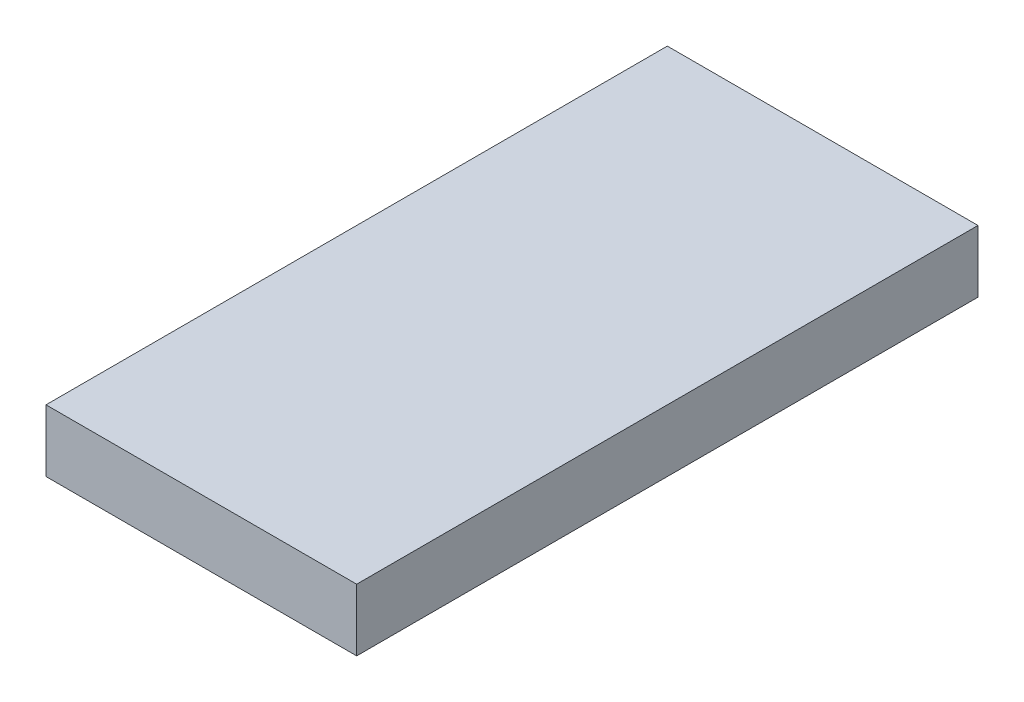
SolidWorks part; units mm, degrees
ref_plane "Front Plane" through (0, 0, 0) normal (0, 0, 1) x (1, 0, 0)
ref_plane "Top Plane" through (0, 0, 0) normal (0, 1, 0) x (1, 0, 0)
ref_plane "Right Plane" through (0, 0, 0) normal (1, 0, 0) x (0, 0, -1)
sketch "Sketch1" plane through (0, 0, 0) normal (0, 1, 0) x (1, 0, 0)
  line L1 (-23.0655, 24.4849) -> (2.3345, 24.4849)
  line L2 (-23.0655, 24.4849) -> (-23.0655, -26.3151)
  line L3 (-23.0655, -26.3151) -> (2.3345, -26.3151)
  line L4 (2.3345, 24.4849) -> (2.3345, -26.3151)
  dimension "D1" = 25.4
  dimension "D2" = 50.8
extrude "Boss-Extrude1" add sketch "Sketch1" along normal blind 5.08
